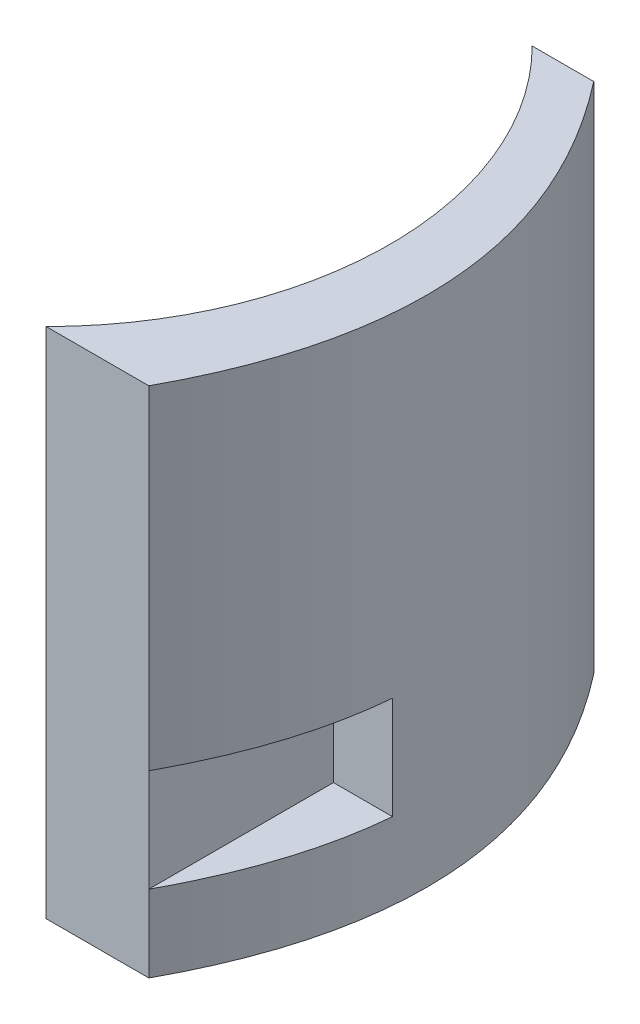
SolidWorks part; units mm, degrees
ref_plane "Front Plane" through (0, 0, 0) normal (0, 0, 1) x (1, 0, 0)
ref_plane "Top Plane" through (0, 0, 0) normal (0, 1, 0) x (1, 0, 0)
ref_plane "Right Plane" through (0, 0, 0) normal (1, 0, 0) x (0, 0, -1)
sketch "Sketch2" plane through (0, 0, 0) normal (0, 1, 0) x (1, 0, 0)
  line L0 (0, 0) -> (-23.6881, 23.6881) construction
  line L1 (0, 0) -> (-23.6881, -23.6881) construction
  line L5 (0, 33.5) -> (0, -33.5) construction
  line L6 (33.5, 0) -> (39.5, 0) construction
  line L7 (23.6881, 23.6881) -> (29.6881, 23.6881)
  line L8 (23.6881, -23.6881) -> (33.6881, -23.6881)
  circle A0 centre (0, 0) radius 33.5
  spline S1 degree 2 poles (29.6881, 23.6881) (47.2217, 1.1836) (33.6881, -23.6881) knots 0 0 0 1 1 1
  point P3 (-23.6881, 23.6881)
  dimension "D1" = 67
  dimension "D5" = 6
  dimension "D6" = 6
  dimension "D7" = 10
extrude "Boss-Extrude1" add sketch "Sketch2" along normal blind 50
sketch "Sketch3" plane through (0, 0, 23.6881) normal (0, 0, 1) x (1, 0, 0)
  line L0 (33.6881, 50) -> (33.6881, 0) construction
  line L1 (33.6881, 7.5) -> (39.6881, 7.5)
  line L2 (33.6881, 7.5) -> (33.6881, 17.5)
  line L3 (33.6881, 17.5) -> (39.6881, 17.5)
  line L4 (39.6881, 7.5) -> (39.6881, 17.5)
  line L5 (23.6881, 0) -> (33.6881, 0) construction
  dimension "D1" = 6
  dimension "D2" = 10
  dimension "D3" = 7.5
extrude "Cut-Extrude1" cut sketch "Sketch3" against normal blind 18
